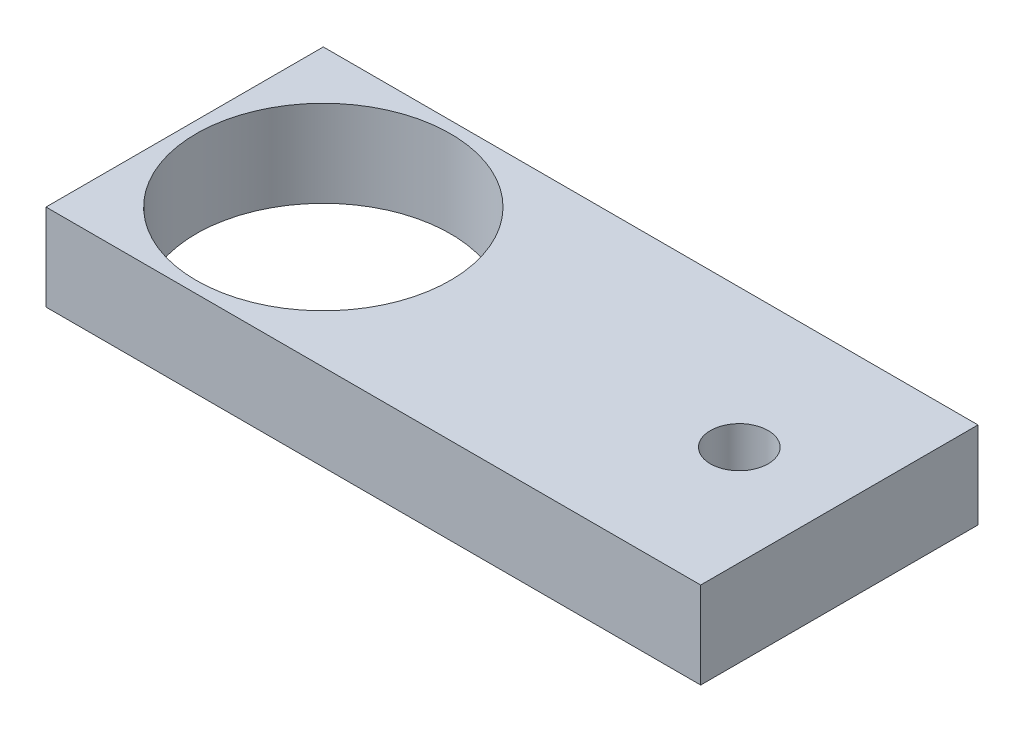
SolidWorks part; units mm, degrees
ref_plane "Front Plane" through (0, 0, 0) normal (0, 0, 1) x (1, 0, 0)
ref_plane "Top Plane" through (0, 0, 0) normal (0, 1, 0) x (1, 0, 0)
ref_plane "Right Plane" through (0, 0, 0) normal (1, 0, 0) x (0, 0, -1)
sketch "Sketch1" plane through (0, 0, 0) normal (0, 1, 0) x (1, 0, 0)
  line L0 (24, 24) -> (91, 24) construction
  line L1 (0, 0) -> (113.3193, 0)
  line L2 (0, 0) -> (0, 48)
  line L3 (0, 48) -> (113.3193, 48)
  line L4 (113.3193, 0) -> (113.3193, 48)
  circle A0 centre (24, 24) radius 22
  circle A1 centre (96, 24) radius 5
extrude "Boss-Extrude1" add sketch "Sketch1" along normal blind 15
